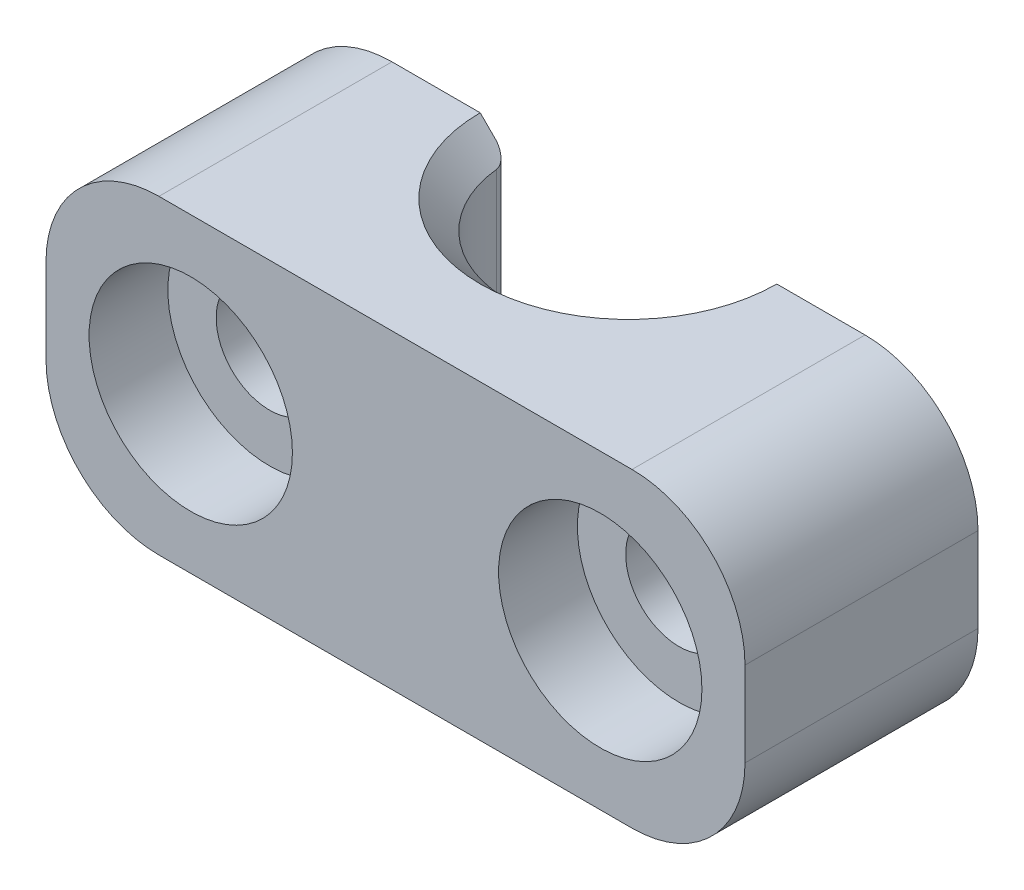
SolidWorks part; units mm, degrees
material "ABS"
ref_plane "Alzado" through (0, 0, 0) normal (0, 0, 1) x (1, 0, 0)
ref_plane "Planta" through (0, 0, 0) normal (0, 1, 0) x (1, 0, 0)
ref_plane "Vista lateral" through (0, 0, 0) normal (1, 0, 0) x (0, 0, -1)
ref_plane "Plano1" through (0, 0, 0) normal (0, 0, -1) x (-1, 0, 0)
sketch "Croquis1" plane through (0, 0, 0) normal (0, 0, -1) x (-1, 0, 0)
  line L0 (-12.375, 5.5) -> (-12.375, -5.5)
  line L1 (-12.375, -5.5) -> (12.375, -5.5)
  line L2 (12.375, -5.5) -> (12.375, 5.5)
  line L3 (12.375, 5.5) -> (-12.375, 5.5)
  point P4 (0, -5.5)
  point P6 (0, 5.5)
  point P7 (12.375, 0)
  point P8 (-12.375, 0)
  dimension "D1" = 11
  dimension "D2" = 24.75
extrude "Saliente-Extruir1" add sketch "Croquis1" against normal blind 8.25
hole_wizard "Refrentado para tornillo con cabeza hexagonal de M3.51" positions "Croquis3" profile "Croquis2" counterbore size "M3.5" standard "Ansi Metric"
sketch "Croquis3" plane through (0, 0, 8.25) normal (0, 0, 1) x (1, 0, 0)
  point P0 (-7.25, 0)
  point P1 (7.25, 0)
sketch "Croquis2" plane through (-7.25, 0, 8.25) normal (1, 0, 0) x (0, -1, 0)
  line L0 (0, 0) -> (0, 8.25)
  line L1 (0, 8.25) -> (1.89, 8.25)
  line L3 (1.89, 8.25) -> (1.89, 2.79)
  line L4 (1.89, 2.79) -> (3.6, 2.79)
  line L5 (3.6, 2.79) -> (3.6, 0)
  line L7 (3.6, 0) -> (0, 0)
  line L11 (0, -6.35) -> (0, 107.95) construction
  dimension "Diámetro de taladro hasta el siguiente" = 3.78
  dimension "Profundidad de taladro hasta el siguiente" = 8.25
  dimension "Diámetro de refrentado" = 7.2
  dimension "Profundidad de refrentado" = 2.79
hole_wizard "Diámetro de taladro Ø8.5 (8.5)1" positions "Croquis5" profile "Croquis4" hole size "Ø8.5" standard "Ansi Metric"
sketch "Croquis5" plane through (0, 5.5, 0) normal (0, 1, 0) x (1, 0, 0)
  point P0 (0, 0)
sketch "Croquis4" plane through (0, 5.5, 0) normal (1, 0, 0) x (0, 0, 1)
  line L0 (0, 0) -> (0, 11)
  line L1 (0, 11) -> (4.25, 11)
  line L2 (4.25, 11) -> (4.25, 0)
  line L5 (4.25, 0) -> (0, 0)
  line L11 (0, -6.35) -> (0, 107.95) construction
  dimension "Diámetro de taladro hasta el siguiente" = 8.5
  dimension "Profundidad de taladro hasta el siguiente" = 11
chamfer "Chaflán1" distance 1 angle 45 2 edges at (0, -5.5, 4.25) (0, 5.5, 4.25)
fillet "Redondeo1" radius 0.5 2 edges at (4.25, 0, 0) (-4.25, 0, 0)
fillet "Redondeo2" radius 4 4 edges at (12.375, -5.5, 4.125) (-12.375, -5.5, 4.125) (12.375, 5.5, 4.125) (-12.375, 5.5, 4.125)
sketch "Croquis6" plane through (0, -5.5, 0) normal (0, -1, 0) x (1, 0, 0)
  circle A0 centre (0, 0) radius 5.25
extrude "Saliente-Extruir2" [suppressed] add sketch "Croquis6" against normal blind 3
